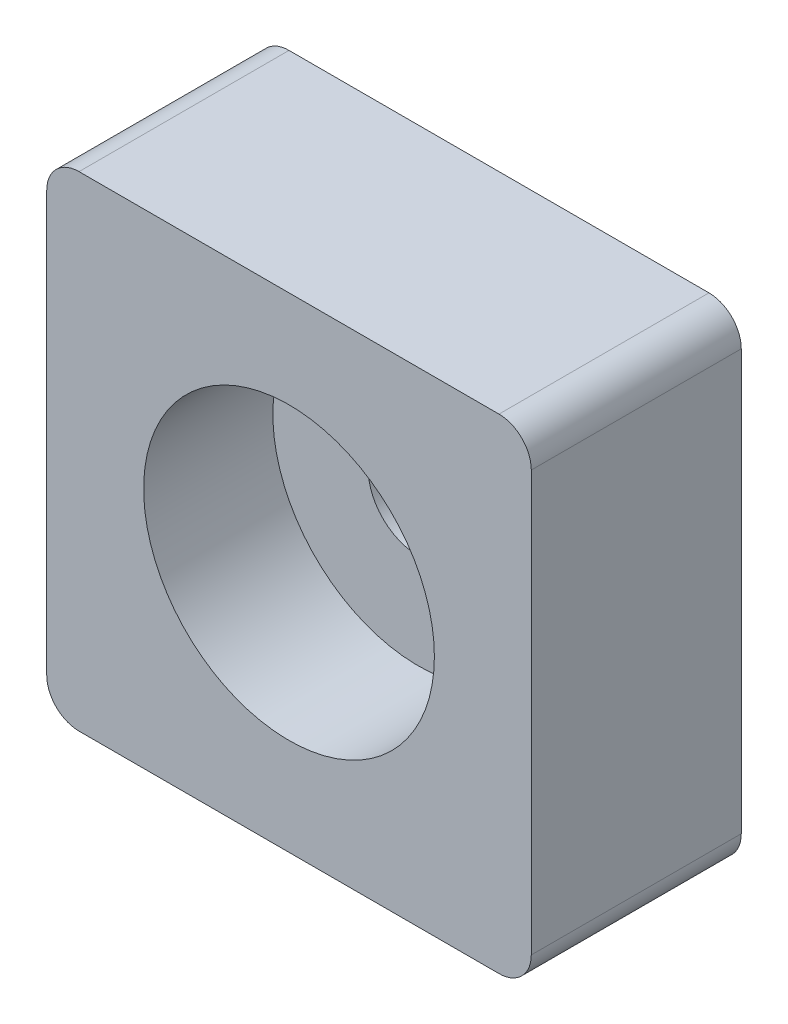
SolidWorks part; units mm, degrees
ref_plane "Front Plane" through (0, 0, 0) normal (0, 0, 1) x (1, 0, 0)
ref_plane "Top Plane" through (0, 0, 0) normal (0, 1, 0) x (1, 0, 0)
ref_plane "Right Plane" through (0, 0, 0) normal (1, 0, 0) x (0, 0, -1)
sketch "Sketch1" plane through (0, 0, 0) normal (0, 0, 1) x (1, 0, 0)
  line L1 (-15, -15) -> (15, -15)
  line L2 (-15, -15) -> (-15, 15)
  line L3 (-15, 15) -> (15, 15)
  line L4 (15, -15) -> (15, 15)
  line L5 (-15, -15) -> (15, 15) construction
  line L6 (-15, 15) -> (15, -15) construction
  circle A0 centre (0, 0) radius 3.1
  point P0 (0, 0)
extrude "Boss-Extrude1" add sketch "Sketch1" along normal blind 13
sketch "Sketch2" plane through (0, 0, 13) normal (0, 0, 1) x (1, 0, 0)
  circle A0 centre (0, 0) radius 9
extrude "Cut-Extrude1" cut sketch "Sketch2" against normal blind 8
fillet "Fillet1" radius 2 4 edges at (-15, 15, 6.5) (15, 15, 6.5) (15, -15, 6.5) (-15, -15, 6.5)
